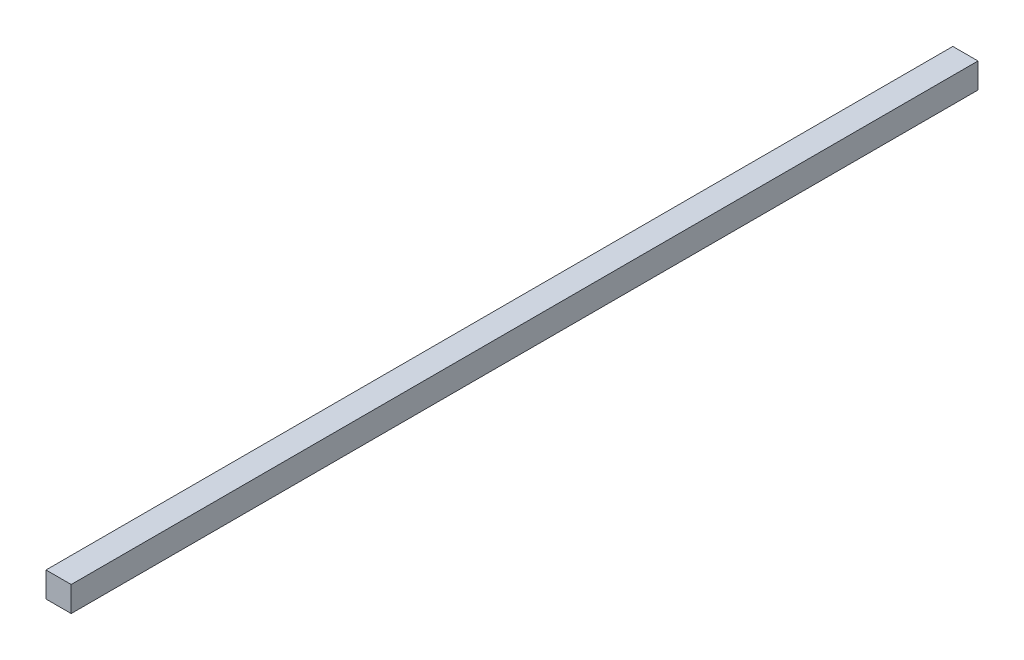
SolidWorks part; units mm, degrees
ref_plane "Front Plane" through (0, 0, 0) normal (0, 0, 1) x (1, 0, 0)
ref_plane "Top Plane" through (0, 0, 0) normal (0, 1, 0) x (1, 0, 0)
ref_plane "Right Plane" through (0, 0, 0) normal (1, 0, 0) x (0, 0, -1)
sketch "Sketch1" plane through (0, 0, 0) normal (0, 0, 1) x (1, 0, 0)
  line L0 (-3.175, 3.175) -> (3.175, -3.175) construction
  line L1 (-3.175, 3.175) -> (3.175, 3.175)
  line L2 (-3.175, 3.175) -> (-3.175, -3.175)
  line L3 (-3.175, -3.175) -> (3.175, -3.175)
  line L4 (3.175, 3.175) -> (3.175, -3.175)
  dimension "D1" = 6.35
  dimension "D2" = 6.35
extrude "Extrude1" add sketch "Sketch1" against normal blind 304.8
sketch "Sketch2" plane through (-3.175, 0, 0) normal (-1, 0, 0) x (0, 0, 1)
  line L0 (-304.8, -3.175) -> (0, -3.175) construction
  line L1 (-304.8, 3.175) -> (-228.6, 3.175)
  line L2 (-304.8, 3.175) -> (-304.8, -3.175)
  line L3 (-304.8, -3.175) -> (-228.6, -3.175)
  line L4 (-228.6, 3.175) -> (-228.6, -3.175)
  line L5 (-228.6, 4.5214) -> (-228.6, -130.0986) construction
extrude "Cut-Extrude1" cut sketch "Sketch2" against normal through all
